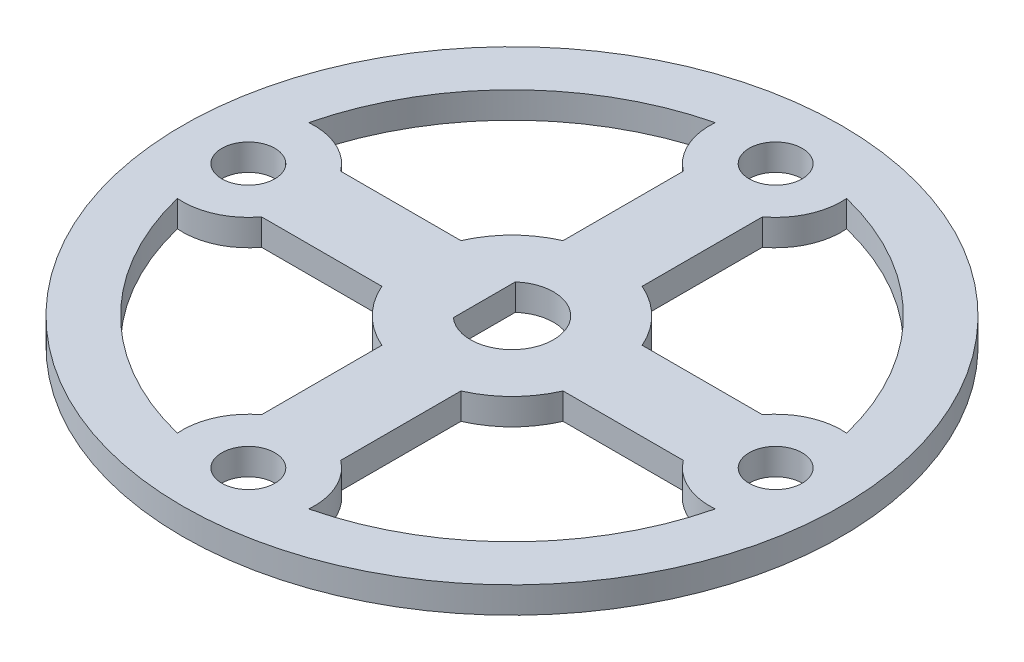
SolidWorks part; units mm, degrees
material "AISI 1020 Steel, Cold Rolled"
ref_plane "Front Plane" through (0, 0, 0) normal (0, 0, 1) x (1, 0, 0)
ref_plane "Top Plane" through (0, 0, 0) normal (0, 1, 0) x (1, 0, 0)
ref_plane "Right Plane" through (0, 0, 0) normal (1, 0, 0) x (0, 0, -1)
other "Bounding Box"
ref_plane "Default Plane" through (0, 2.286, 19.05) normal (0, -1, 0) x (-1, 0, 0)
sketch "Sketch1" plane through (0, 0, 0) normal (0, 1, 0) x (1, 0, 0)
  circle A0 centre (0, 0) radius 4
  circle A1 centre (0, 0) radius 31.75
  dimension "D1" = 8
  dimension "D2" = 63.5
extrude "Boss-Extrude1" add sketch "Sketch1" along normal mid plane 2.54
sketch "Sketch2" plane through (0, 1.27, 0) normal (0, 1, 0) x (1, 0, 0)
  line L0 (-2.667, -2.9811) -> (-2.667, 2.9811)
  arc A0 (-2.667, 2.9811) -> (-2.667, -2.9811) centre (0, 0) ccw
  circle A1 centre (0, 0) radius 4 construction
  dimension "D1" = 2.667
extrude "Boss-Extrude3" add sketch "Sketch2" against normal through all
sketch "Sketch3" plane through (0, 1.27, 0) normal (0, 1, 0) x (1, 0, 0)
  line L0 (0, 0) -> (0, 25.4) construction
  circle A0 centre (0, 25.4) radius 2.5527
  dimension "D1" = 5.1054
  dimension "D2" = 25.4
extrude "Cut-Extrude1" cut sketch "Sketch3" against normal through all
sketch "Sketch4" plane through (0, 1.27, 0) normal (0, 1, 0) x (1, 0, 0)
  line L0 (3.81, 8.7298) -> (3.81, 20.32)
  line L1 (8.7298, 3.81) -> (20.32, 3.81)
  line L2 (0, 0) -> (0, 31.75) construction
  line L3 (0, 0) -> (31.75, 0) construction
  line L4 (3.81, 14.5249) -> (0, 14.5249) construction
  line L5 (14.5249, 3.81) -> (14.5249, 0) construction
  arc A0 (6.3296, 25.908) -> (25.908, 6.3296) centre (0, 0) cw
  arc A1 (6.3296, 25.908) -> (3.81, 20.32) centre (0, 25.4) cw
  arc A2 (25.908, 6.3296) -> (20.32, 3.81) centre (25.4, 0) ccw
  arc A3 (3.81, 8.7298) -> (8.7298, 3.81) centre (0, 0) cw
  circle A4 centre (0, 0) radius 31.75 construction
  circle A5 centre (0, 0) radius 25.4 construction
  dimension "D2" = 9.525
  dimension "D3" = 6.35
  dimension "D4" = 5.08
  dimension "D1" = 3.81
extrude "Cut-Extrude2" cut sketch "Sketch4" against normal through all
pattern_circular "CirPattern1" count 4 over 360 about axis through (0, 0, 0) along (0, 1, 0) of "Cut-Extrude2", "Cut-Extrude1"
equation "\"Unit Measure\"= \"BoundingVolume\" / \"Thickness\"'in^2"
